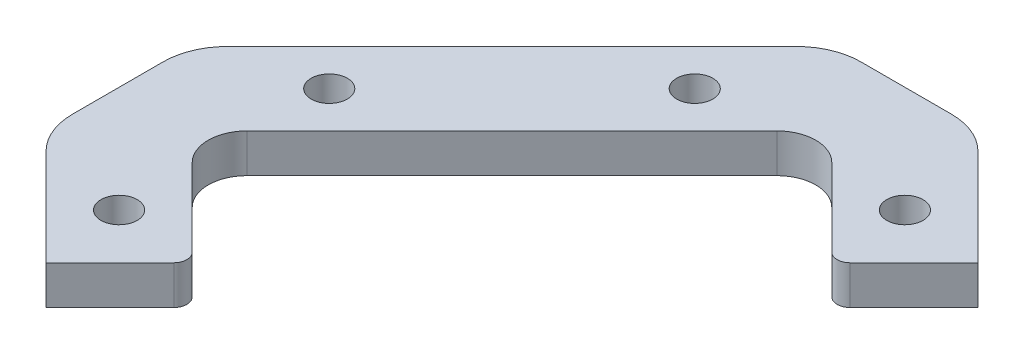
SolidWorks part; units mm, degrees
ref_plane "Front Plane" through (0, 0, 0) normal (0, 0, 1) x (1, 0, 0)
ref_plane "Top Plane" through (0, 0, 0) normal (0, 1, 0) x (1, 0, 0)
ref_plane "Right Plane" through (0, 0, 0) normal (1, 0, 0) x (0, 0, -1)
sketch "Sketch1" plane through (0, 0, 0) normal (0, 1, 0) x (1, 0, 0)
  line L0 (-6.0375, -13.9247) -> (-12.0479, -7.9143)
  line L1 (-12.0479, -3.6716) -> (8.4582, 16.8345)
  line L2 (12.7009, 16.8345) -> (18.7113, 10.8241)
  line L3 (20.1255, 10.8241) -> (25.0752, 15.7738)
  line L4 (25.0752, 15.7738) -> (17.6065, 23.2426)
  line L5 (14.0709, 24.707) -> (7.0882, 24.707)
  line L6 (3.5526, 23.2426) -> (-18.456, 1.234)
  line L7 (-19.9204, -2.3016) -> (-19.9204, -9.2843)
  line L8 (-18.456, -12.8199) -> (-10.9872, -20.2886)
  line L9 (-10.9872, -20.2886) -> (-6.0375, -15.3389)
  circle A0 centre (18.7113, 16.4809) radius 1.4
  circle A1 centre (2.4478, 16.4809) radius 1.4
  circle A2 centre (-11.6943, 2.3388) radius 1.4
  circle A3 centre (-11.6943, -13.9247) radius 1.4
  arc A4 (-6.0375, -15.3389) -> (-6.0375, -13.9247) centre (-6.7446, -14.6318) ccw
  arc A5 (-12.0479, -3.6716) -> (-12.0479, -7.9143) centre (-9.9265, -5.793) ccw
  arc A6 (12.7009, 16.8345) -> (8.4582, 16.8345) centre (10.5796, 14.7131) ccw
  arc A7 (18.7113, 10.8241) -> (20.1255, 10.8241) centre (19.4184, 11.5312) ccw
  arc A8 (17.6065, 23.2426) -> (14.0709, 24.707) centre (14.0709, 19.707) ccw
  arc A9 (7.0882, 24.707) -> (3.5526, 23.2426) centre (7.0882, 19.707) ccw
  arc A10 (-18.456, 1.234) -> (-19.9204, -2.3016) centre (-14.9204, -2.3016) ccw
  arc A11 (-19.9204, -9.2843) -> (-18.456, -12.8199) centre (-14.9204, -9.2843) ccw
  dimension "D1" = 2.8
  dimension "D2" = 51
extrude "Boss-Extrude1" add sketch "Sketch1" along normal blind 3
